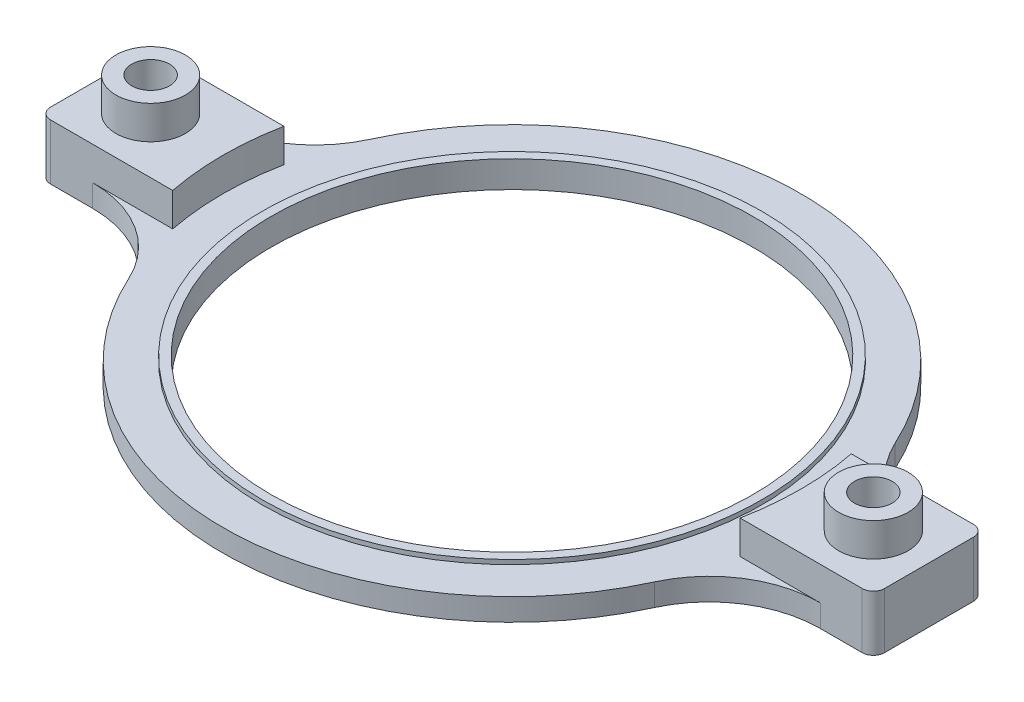
SolidWorks part; units mm, degrees
ref_plane "Front Plane" through (0, 0, 0) normal (0, 0, 1) x (1, 0, 0)
ref_plane "Top Plane" through (0, 0, 0) normal (0, 1, 0) x (1, 0, 0)
ref_plane "Right Plane" through (0, 0, 0) normal (1, 0, 0) x (0, 0, -1)
sketch "Sketch1" plane through (0, 0, 0) normal (0, 1, 0) x (1, 0, 0)
  circle A0 centre (0, 0) radius 26
  circle A1 centre (0, 0) radius 21.675
  dimension "D1" = 52
  dimension "D2" = 43.35
extrude "Boss-Extrude1" add sketch "Sketch1" along normal blind 2
sketch "Sketch2" plane through (0, 2, 0) normal (0, 1, 0) x (1, 0, 0)
  circle A0 centre (0, 0) radius 22.475
  circle A1 centre (0, 0) radius 21.675 construction
  circle A2 centre (0, 0) radius 21.675
  dimension "D1" = 44.95
extrude "Boss-Extrude2" add sketch "Sketch2" along normal blind 0.4
sketch "Sketch3" plane through (0, 0, 0) normal (0, -1, 0) x (1, 0, 0)
  line L0 (0, 0) -> (36.065, 0) construction
  line L1 (25.5147, -5) -> (27.5147, -5)
  line L2 (25.5147, 5) -> (27.5147, 5)
  line L3 (27.5147, -5) -> (27.5147, 5)
  circle A0 centre (0, 0) radius 26 construction
  arc A1 (25.5147, -5) -> (25.5147, 5) centre (0, 0) ccw
  dimension "D1" = 10
  dimension "D2" = 2
extrude "Boss-Extrude3" add sketch "Sketch3" against normal blind 5
sketch "Sketch4" plane through (27.5147, 0, 0) normal (1, 0, 0) x (0, 0, -1)
  line L0 (5, 5) -> (5, 0) construction
  line L1 (5, 3) -> (-5, 3)
  line L2 (5, 3) -> (5, 5)
  line L3 (5, 5) -> (-5, 5)
  line L4 (-5, 3) -> (-5, 5)
  dimension "D1" = 2
extrude "Boss-Extrude4" add sketch "Sketch4" along normal blind 9.9853
sketch "Sketch5" plane through (0, 3, 0) normal (0, -1, 0) x (1, 0, 0)
  line L0 (37.5, 0) -> (27.5147, 0) construction
  line L1 (37.5, 5) -> (37.5, -5) construction
  line L2 (27.5147, -5) -> (27.5147, 5) construction
  line L3 (27.5147, 5) -> (27.5147, -5) construction
  circle A0 centre (32.5, 0) radius 3.125
  dimension "D1" = 4.9853
  dimension "D2" = 6.25
extrude "Boss-Extrude7" add sketch "Sketch5" against normal blind 5
sketch "Sketch7" plane through (0, 3, 0) normal (0, -1, 0) x (1, 0, 0)
  circle A0 centre (32.5, 0) radius 3.125 construction
  circle A1 centre (32.5, 0) radius 3.125 construction
  point P0 (32.5, 0)
hole_wizard "M3 Clearance Hole1" positions "Sketch7" profile "Sketch8" hole size "M3" standard "ANSI Metric" end condition through all
sketch "Sketch8" plane through (32.5, 3, 0) normal (1, 0, 0) x (0, 0, -1)
  line L0 (0, 0) -> (0, 5)
  line L1 (0, 5) -> (1.7, 5)
  line L2 (1.7, 5) -> (1.7, 0)
  line L5 (1.7, 0) -> (0, 0)
  line L11 (0, -6.35) -> (0, 107.95) construction
  dimension "Thru Hole Dia." = 3.4
  dimension "Thru Hole Depth" = 5
mirror "Mirror1" about plane through (0, 0, 0) normal (1, 0, 0) of "Boss-Extrude3", "M3 Clearance Hole1", "Boss-Extrude7", "Boss-Extrude4"
fillet "Fillet1" radius 1 4 edges at (-37.5, 4, -5) (-37.5, 4, 5) (37.5, 4, 5) (37.5, 4, -5)
fillet "Fillet2" [suppressed] radius 11
sketch "Sketch9" plane through (0, 3, 0) normal (0, -1, 0) x (1, 0, 0)
  line L4 (-37.5, 4) -> (-37.5, -4)
  line L5 (-36.5, -5) -> (-27.5147, -5)
  line L6 (-27.5147, -5) -> (-27.5147, 5)
  line L7 (-27.5147, 5) -> (-36.5, 5)
  line L8 (-37.5, 4) -> (-37.5, -4)
  line L9 (-36.5, -5) -> (-27.5147, -5)
  line L10 (-27.5147, -5) -> (-27.5147, 5)
  line L11 (-27.5147, 5) -> (-36.5, 5)
  line L12 (37.5, -4) -> (37.5, 4)
  line L13 (36.5, 5) -> (27.5147, 5)
  line L14 (27.5147, 5) -> (27.5147, -5)
  line L15 (27.5147, -5) -> (36.5, -5)
  line L16 (37.5, -4) -> (37.5, 4)
  line L17 (36.5, 5) -> (27.5147, 5)
  line L18 (27.5147, 5) -> (27.5147, -5)
  line L19 (27.5147, -5) -> (36.5, -5)
  circle A0 centre (32.5, 0) radius 1.7 construction
  circle A1 centre (-32.5, 0) radius 1.7 construction
  arc A2 (-37.5, -4) -> (-36.5, -5) centre (-36.5, -4) ccw
  arc A3 (-36.5, 5) -> (-37.5, 4) centre (-36.5, 4) ccw
  arc A4 (-37.5, -4) -> (-36.5, -5) centre (-36.5, -4) ccw
  arc A5 (-36.5, 5) -> (-37.5, 4) centre (-36.5, 4) ccw
  arc A6 (37.5, 4) -> (36.5, 5) centre (36.5, 4) ccw
  arc A7 (36.5, -5) -> (37.5, -4) centre (36.5, -4) ccw
  arc A8 (37.5, 4) -> (36.5, 5) centre (36.5, 4) ccw
  arc A9 (36.5, -5) -> (37.5, -4) centre (36.5, -4) ccw
  circle A10 centre (32.5, 0) radius 1.7
  circle A11 centre (-32.5, 0) radius 1.7
  dimension "D1" = 0
  dimension "D2" = 0
extrude "Boss-Extrude8" add sketch "Sketch9" along normal through all
fillet "Fillet3" radius 10 4 edges at (-25.5147, 1, 5) (-25.5147, 1, -5) (25.5147, 1, -5) (25.5147, 1, 5)
